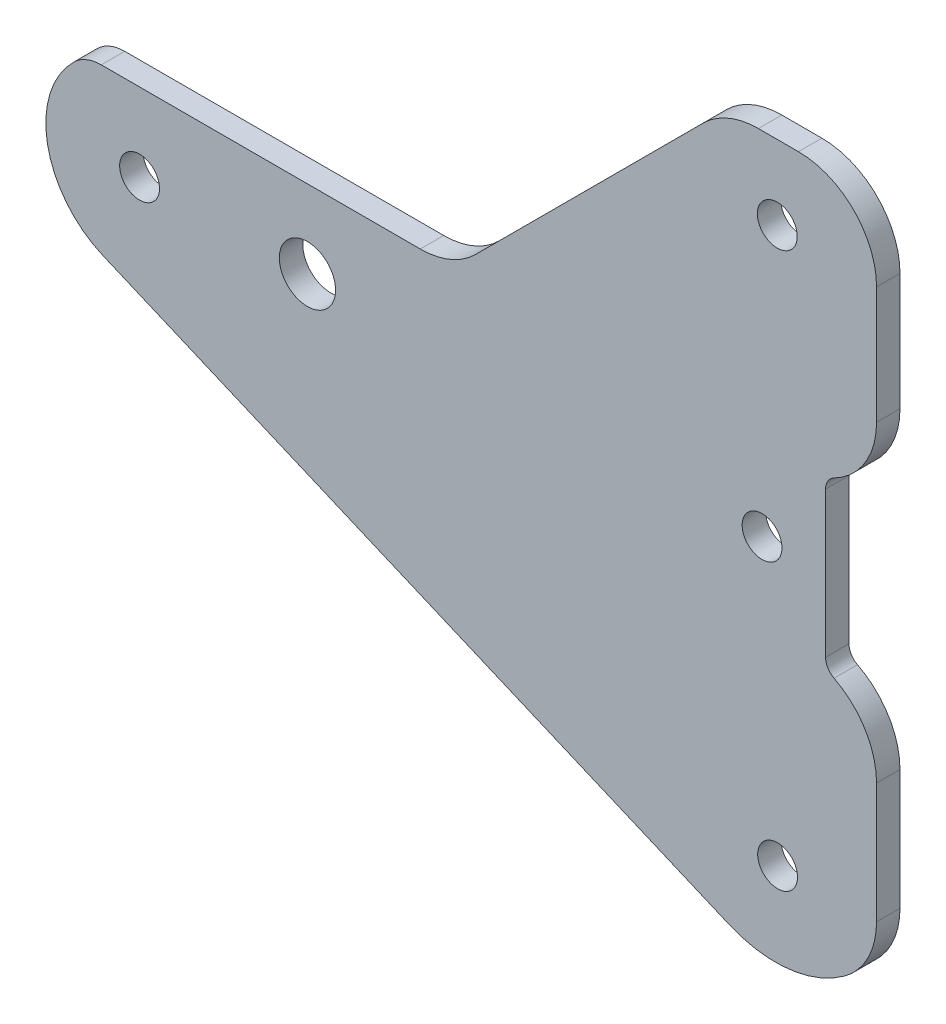
SolidWorks part; units mm, degrees
ref_plane "Front Plane" through (0, 0, 0) normal (0, 0, 1) x (1, 0, 0)
ref_plane "Top Plane" through (0, 0, 0) normal (0, 1, 0) x (1, 0, 0)
ref_plane "Right Plane" through (0, 0, 0) normal (1, 0, 0) x (0, 0, -1)
sketch "Sketch1" plane through (0, 0, 0) normal (0, 0, 1) x (1, 0, 0)
  line L0 (-40.3202, 38.0967) -> (0.5198, 38.0967)
  line L1 (7.5908, 41.0256) -> (36.7307, 70.1655)
  line L2 (43.8018, 73.0944) -> (48.9318, 73.0944)
  line L3 (-40.1159, 17.053) -> (40.1159, -17.053)
  line L4 (58.9318, 59.0599) -> (58.9318, -4.9215) construction
  line L5 (58.9318, -7.2872) -> (58.9318, 8.0928)
  line L6 (52.4018, 18.7736) -> (52.4018, 37.4136)
  line L7 (58.9318, 48.0944) -> (58.9318, 63.0944)
  line L8 (52.4018, 34.0622) -> (52.4018, 20.5649) construction
  arc A0 (-40.3202, 38.0967) -> (-43.8194, 36.6682) centre (-40.3202, 33.0967) ccw
  arc A1 (-43.8194, 36.6682) -> (-40.1159, 17.053) centre (-35.4213, 28.0966) ccw
  arc A2 (7.5908, 41.0256) -> (0.5198, 38.0967) centre (0.5198, 48.0967) cw
  arc A3 (36.7307, 70.1655) -> (43.8018, 73.0944) centre (43.8018, 63.0944) cw
  arc A4 (40.1159, -17.053) -> (54.8272, -15.3645) centre (45.9841, -3.2485) ccw
  arc A5 (54.8272, -15.3645) -> (58.9318, -7.2872) centre (48.9318, -7.2872) ccw
  arc A6 (58.9318, 8.0928) -> (53.4901, 16.9935) centre (48.9318, 8.0928) ccw
  arc A7 (53.4901, 16.9935) -> (52.4018, 18.7736) centre (54.4018, 18.7736) cw
  arc A8 (52.4018, 37.4136) -> (53.4901, 39.1937) centre (54.4018, 37.4136) cw
  arc A9 (53.4901, 39.1937) -> (58.9318, 48.0944) centre (48.9318, 48.0944) ccw
  arc A10 (58.9318, 63.0944) -> (48.9318, 73.0944) centre (48.9318, 63.0944) ccw
  circle A11 centre (-35.4213, 28.0966) radius 2.55
  circle A12 centre (-13.9313, 28.0966) radius 3.6
  circle A13 centre (46.2218, 63.5944) radius 2.55
  circle A14 centre (44.2718, 28.0944) radius 2.55
  circle A15 centre (46.2646, -7.409) radius 2.55
  point P13 (4.6619, 38.0967)
  dimension "D2" = 5
  dimension "D3" = 12
  dimension "D7" = 10
  dimension "D9" = 10
  dimension "D10" = 15
  dimension "D11" = 10
  dimension "D12" = 15.38
  dimension "D13" = 10
  dimension "D14" = 2
  dimension "D15" = 10
  dimension "D16" = 2
  dimension "D17" = 10
  dimension "D22" = 5.1
  dimension "D23" = 7.2
  dimension "D25" = 5.1
  dimension "D28" = 5.1
  dimension "D31" = 5.1
  dimension "D1" = 135
  dimension "D4" = 23.03
  dimension "D5" = 40.84
  dimension "D6" = 87.18
  dimension "D8" = 41.21
  dimension "D18" = 15
  dimension "D19" = 5.13
  dimension "D20" = 6.53
  dimension "D21" = 18.64
  dimension "D24" = 21.49
  dimension "D26" = 9.5
  dimension "D27" = 2.71
  dimension "D29" = 8.13
  dimension "D30" = 45
  dimension "D32" = 2.67
  dimension "D33" = 4.17
extrude "Boss-Extrude1" add sketch "Sketch1" along normal blind 3
